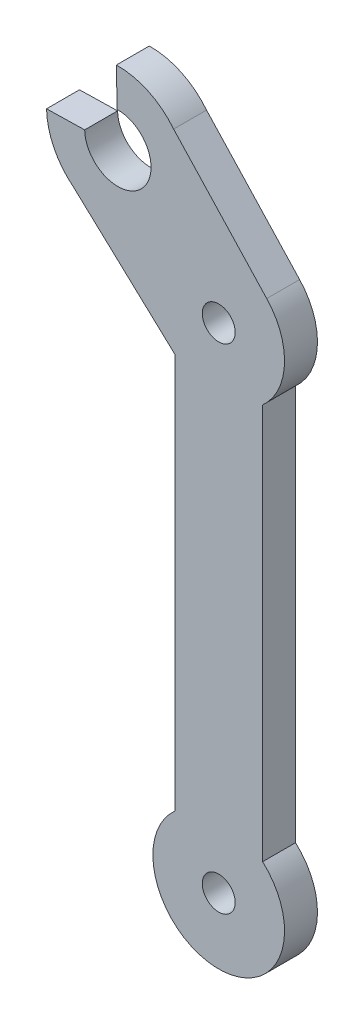
SolidWorks part; units mm, degrees
ref_plane "Plan de face" through (0, 0, 0) normal (0, 0, 1) x (1, 0, 0)
ref_plane "Plan de dessus" through (0, 0, 0) normal (0, 1, 0) x (1, 0, 0)
ref_plane "Plan de droite" through (0, 0, 0) normal (1, 0, 0) x (0, 0, -1)
sketch "Esquisse1" plane through (0, 0, 0) normal (0, 0, 1) x (1, 0, 0)
  line L0 (4, 45) -> (4, 0) construction
  line L1 (-2.1681, 54.2562) -> (-5.1924, 54.1924)
  line L2 (0, 0) -> (0, 40.5279)
  line L3 (-5.2562, 57.2167) -> (-5.3995, 64.0091)
  line L4 (8, 0) -> (8, 40.5279)
  line L5 (4, 45) -> (-5.1924, 54.1924) construction
  line L6 (4, 45) -> (-4.5188, 53.5188) construction
  line L7 (0, 40.5279) -> (-9.2413, 49.1075)
  line L8 (-8.2167, 54.1286) -> (-11.6909, 54.0553)
  line L9 (-2.2504, 47.4647) -> (-2.2931, 47.4815) construction
  line L11 (-0.1075, 58.2413) -> (8.3736, 49.1075)
  arc A0 (8, 40.5279) -> (8.3736, 49.1075) centre (4, 45) ccw
  arc A1 (0, 4.4721) -> (8, 4.4721) centre (4, 0) ccw
  circle A2 centre (4, 45) radius 1.5
  circle A3 centre (4, 0) radius 1.5
  arc A4 (-8.2167, 54.1286) -> (-5.2562, 57.2167) centre (-5.1924, 54.1924) ccw
  arc A5 (-0.1075, 58.2413) -> (-5.3295, 60.6909) centre (-5.1924, 54.1924) ccw
  arc A6 (-0.1632, 40.6794) -> (0, 40.5279) centre (4, 45) ccw
  arc A7 (-11.6909, 54.0553) -> (-9.2413, 49.1075) centre (-5.1924, 54.1924) ccw
  dimension "D3" = 12
  dimension "D4" = 12
  dimension "D5" = 3
  dimension "D6" = 3
  dimension "D9" = 6.05
  dimension "D10" = 13
  dimension "D2" = 8
  dimension "D7" = 135
  dimension "D8" = 13
  dimension "D11" = 90
extrude "Boss.-Extru.1" add sketch "Esquisse1" along normal blind 3
